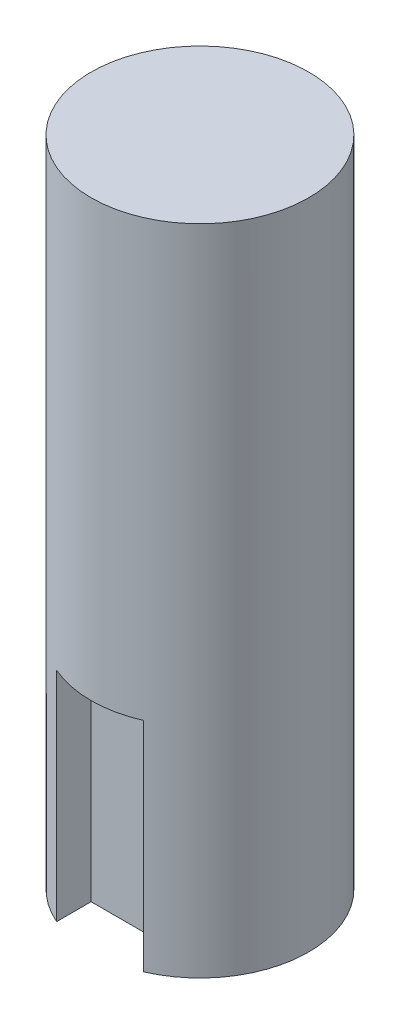
SolidWorks part; units mm, degrees
ref_plane "Front Plane" through (0, 0, 0) normal (0, 0, 1) x (1, 0, 0)
ref_plane "Top Plane" through (0, 0, 0) normal (0, 1, 0) x (1, 0, 0)
ref_plane "Right Plane" through (0, 0, 0) normal (1, 0, 0) x (0, 0, -1)
sketch "Sketch1" plane through (0, 0, 0) normal (0, 1, 0) x (1, 0, 0)
  circle A0 centre (0, 0) radius 5
  dimension "D1" = 10
extrude "Boss-Extrude1" add sketch "Sketch1" along normal blind 30
sketch "Sketch2" plane through (0, 0, 0) normal (0, -1, 0) x (1, 0, 0)
  line L1 (-2, 3) -> (2, 3)
  line L2 (-2, 3) -> (-2, 4.5826)
  line L4 (2, 3) -> (2, 4.5826)
  line L5 (-2, 3) -> (0, 5) construction
  line L6 (0, 5) -> (2, 3) construction
  circle A0 centre (0, 0) radius 5 construction
  arc A1 (2, 4.5826) -> (-2, 4.5826) centre (0, 0) ccw
  point P0 (0, 5)
  dimension "D1" = 1.5826
  dimension "D2" = 4
extrude "Cut-Extrude1" cut sketch "Sketch2" against normal blind 10
